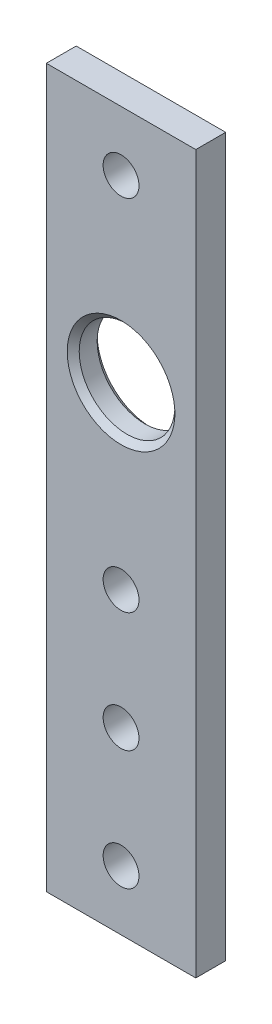
SolidWorks part; units mm, degrees
ref_plane "Front Plane" through (0, 0, 0) normal (0, 0, 1) x (1, 0, 0)
ref_plane "Top Plane" through (0, 0, 0) normal (0, 1, 0) x (1, 0, 0)
ref_plane "Right Plane" through (0, 0, 0) normal (1, 0, 0) x (0, 0, -1)
sketch "Sketch1" plane through (0, 0, 0) normal (0, 0, 1) x (1, 0, 0)
  line L0 (12.5, 120) -> (12.5, 0) construction
  line L1 (0, 0) -> (25, 0)
  line L2 (0, 0) -> (0, 120)
  line L3 (0, 120) -> (25, 120)
  line L4 (25, 0) -> (25, 120)
  circle A0 centre (12.5, 110) radius 3
  circle A1 centre (12.5, 80) radius 8
  circle A2 centre (12.5, 50) radius 3
  circle A3 centre (12.5, 30) radius 3
  circle A4 centre (12.5, 10) radius 3
  dimension "D3" = 6
  dimension "D4" = 16
  dimension "D1" = 25
  dimension "D2" = 120
  dimension "D5" = 10
  dimension "D6" = 20
  dimension "D7" = 20
  dimension "D8" = 30
  dimension "D9" = 30
extrude "Boss-Extrude1" add sketch "Sketch1" along normal blind 5
chamfer "Chamfer1" distance 1 angle 45 2 edges at (20.5, 80, 0) (20.5, 80, 5)
